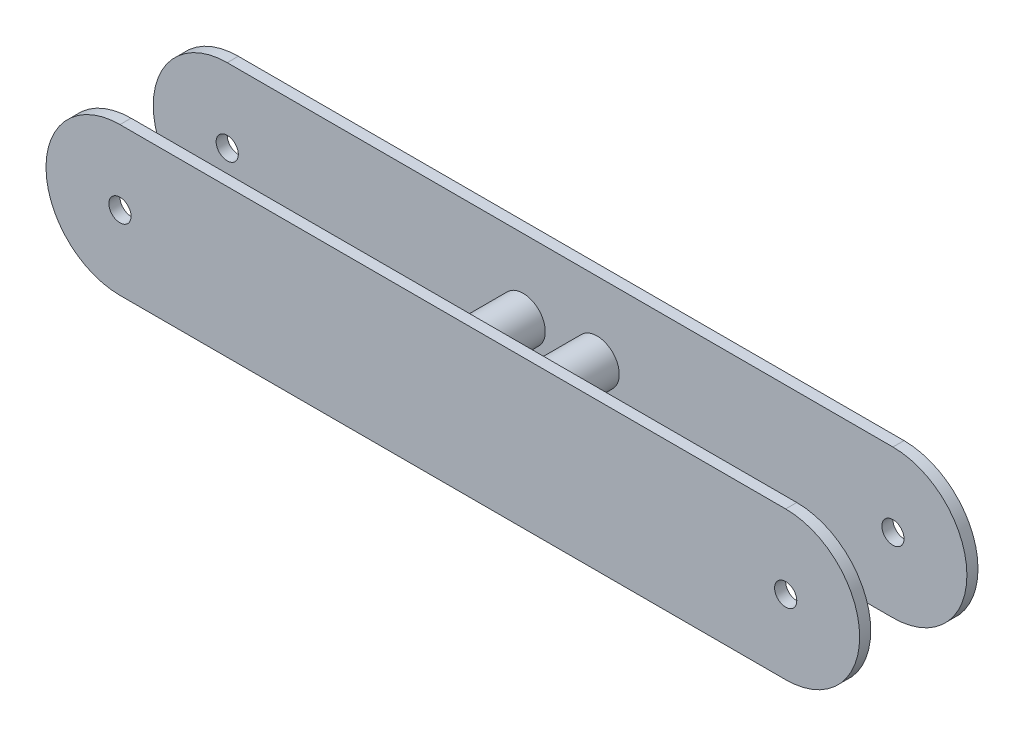
SolidWorks part; units mm, degrees
ref_plane "Front Plane" through (0, 0, 0) normal (0, 0, 1) x (1, 0, 0)
ref_plane "Top Plane" through (0, 0, 0) normal (0, 1, 0) x (1, 0, 0)
ref_plane "Right Plane" through (0, 0, 0) normal (1, 0, 0) x (0, 0, -1)
sketch "Sketch1" plane through (0, 0, 0) normal (0, 0, 1) x (1, 0, 0)
  line L1 (-3.7451, 2.0995) -> (86.2549, 2.0995)
  line L2 (-3.7451, 2.0995) -> (-3.7451, -17.9005)
  line L3 (-3.7451, -17.9005) -> (86.2549, -17.9005)
  line L4 (86.2549, 2.0995) -> (86.2549, -17.9005)
  arc A0 (-3.7451, 2.0995) -> (-3.7451, -17.9005) centre (-3.7451, -7.9005) ccw
  arc A1 (86.2549, 2.0995) -> (86.2549, -17.9005) centre (86.2549, -7.9005) cw
  dimension "D1" = 90
  dimension "D2" = 20
extrude "Boss-Extrude2" add sketch "Sketch1" along normal blind 16 contours L2 A0 | L4 L1 L2 L3 | A1 L4
sketch "Sketch2" plane through (0, 0, 16) normal (0, 0, 1) x (1, 0, 0)
  circle A0 centre (-3.7451, -7.9005) radius 1.5
  circle A1 centre (86.2549, -7.9005) radius 1.5
extrude "Cut-Extrude1" cut sketch "Sketch2" against normal blind 16
sketch "Sketch3" plane through (0, 2.0995, 0) normal (0, 1, 0) x (1, 0, 0)
  line L0 (-3.7451, -16) -> (86.2549, -16) construction
  line L1 (-13.7605, -14.5) -> (96.2762, -14.5)
  line L2 (-13.7605, -14.5) -> (-13.7605, -1.5)
  line L3 (-13.7605, -1.5) -> (96.2762, -1.5)
  line L4 (96.2762, -14.5) -> (96.2762, -1.5)
  line L5 (-3.7451, 0) -> (86.2549, 0) construction
  dimension "D1" = 1.5
  dimension "D2" = 1.5
extrude "Cut-Extrude2" cut sketch "Sketch3" against normal blind 23
sketch "Sketch4" plane through (0, 0, 0) normal (0, 0, -1) x (-1, 0, 0)
  line L0 (3.7451, 2.0995) -> (-86.2549, 2.0995) construction
  circle A0 centre (-36.2549, -7.9005) radius 3
  circle A1 centre (-46.2549, -7.9005) radius 3
  arc A2 (-86.2549, 2.0995) -> (-86.2549, -17.9005) centre (-86.2549, -7.9005) ccw construction
  dimension "D4" = 40
  dimension "D1" = 10
  dimension "D2" = 10
  dimension "D3" = 10
extrude "Boss-Extrude3" add sketch "Sketch4" against normal blind 16
